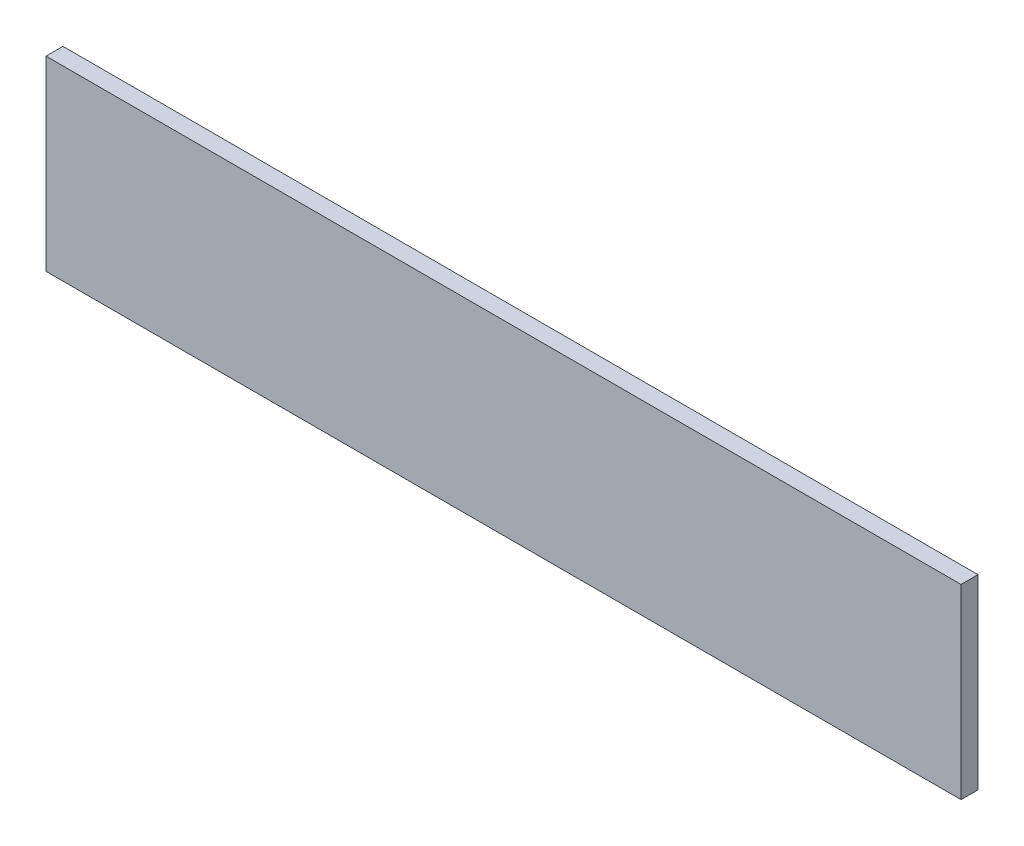
SolidWorks part; units mm, degrees
ref_plane "Front Plane" through (0, 0, 0) normal (0, 0, 1) x (1, 0, 0)
ref_plane "Top Plane" through (0, 0, 0) normal (0, 1, 0) x (1, 0, 0)
ref_plane "Right Plane" through (0, 0, 0) normal (1, 0, 0) x (0, 0, -1)
sketch "Sketch1" plane through (0, 0, 0) normal (0, 0, 1) x (1, 0, 0)
  line L1 (-342.9, 69.85) -> (342.9, 69.85)
  line L2 (-342.9, 69.85) -> (-342.9, -69.85)
  line L3 (-342.9, -69.85) -> (342.9, -69.85)
  line L4 (342.9, 69.85) -> (342.9, -69.85)
  line L5 (-342.9, 69.85) -> (342.9, -69.85) construction
  line L6 (-342.9, -69.85) -> (342.9, 69.85) construction
  point P0 (0, 0)
  dimension "D1" = 685.8
  dimension "D2" = 139.7
extrude "Boss-Extrude1" add sketch "Sketch1" along normal blind 12.7
